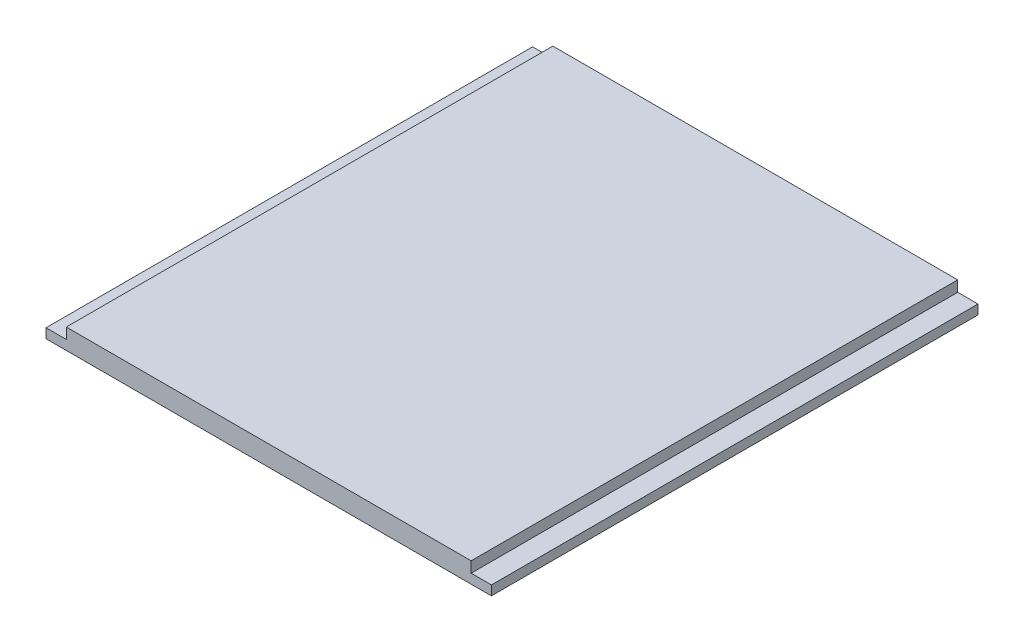
SolidWorks part; units mm, degrees
ref_plane "Front Plane" through (0, 0, 0) normal (0, 0, 1) x (1, 0, 0)
ref_plane "Top Plane" through (0, 0, 0) normal (0, 1, 0) x (1, 0, 0)
ref_plane "Right Plane" through (0, 0, 0) normal (1, 0, 0) x (0, 0, -1)
sketch "Sketch1" plane through (0, 0, 0) normal (0, 1, 0) x (1, 0, 0)
  line L1 (0, 0) -> (139.5, 0)
  line L2 (0, 0) -> (0, 152.4)
  line L3 (0, 152.4) -> (139.5, 152.4)
  line L4 (139.5, 0) -> (139.5, 152.4)
  dimension "D1" = 152.4
  dimension "D2" = 139.5
extrude "Boss-Extrude1" add sketch "Sketch1" along normal blind 6.35
sketch "Sketch2" plane through (0, 6.35, 0) normal (0, 1, 0) x (1, 0, 0)
  line L0 (0, 0) -> (139.5, 0) construction
  line L1 (0, 152.4) -> (6.35, 152.4)
  line L2 (0, 152.4) -> (0, 0)
  line L3 (0, 0) -> (6.35, 0)
  line L4 (6.35, 152.4) -> (6.35, 0)
  line L6 (139.5, 152.4) -> (133.15, 152.4)
  line L7 (139.5, 152.4) -> (139.5, 0)
  line L8 (139.5, 0) -> (133.15, 0)
  line L9 (133.15, 152.4) -> (133.15, 0)
  dimension "D1" = 6.35
  dimension "D2" = 6.35
extrude "Cut-Extrude1" cut sketch "Sketch2" against normal blind 3.375
